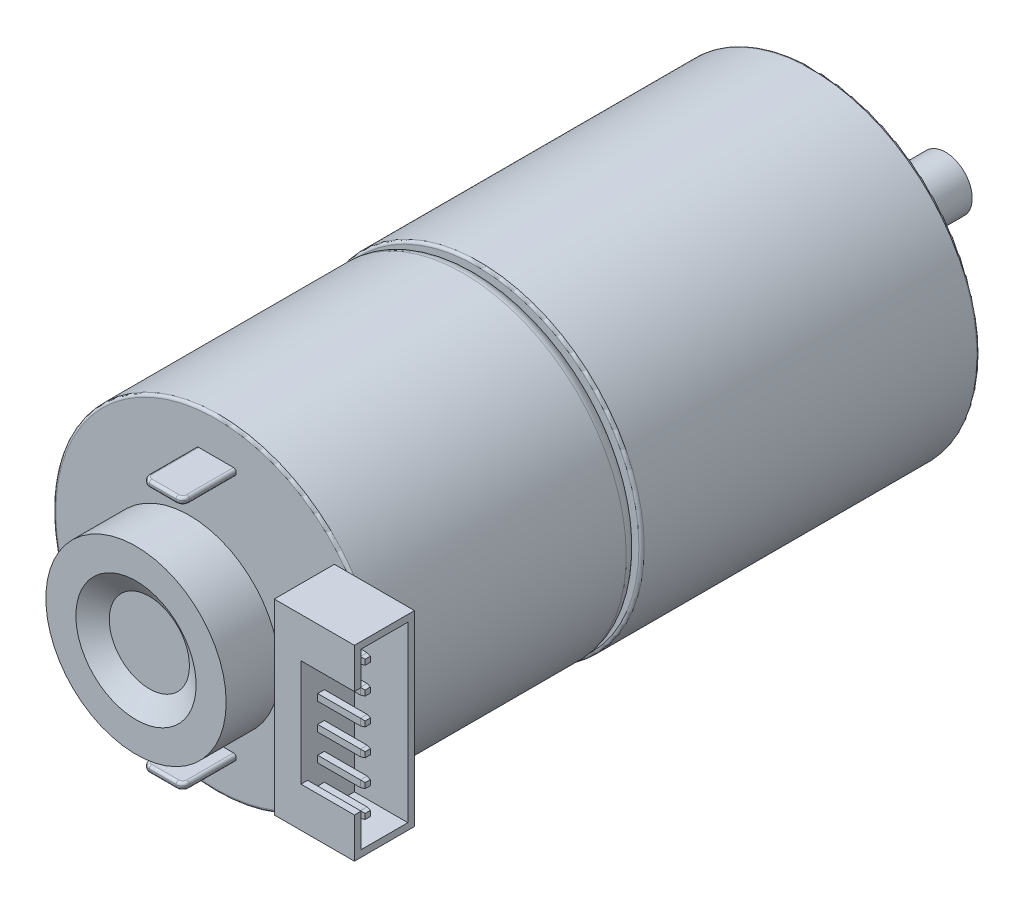
SolidWorks part; units mm, degrees
ref_plane "Front Plane" through (0, 0, 0) normal (0, 0, 1) x (1, 0, 0)
ref_plane "Top Plane" through (0, 0, 0) normal (0, 1, 0) x (1, 0, 0)
ref_plane "Right Plane" through (0, 0, 0) normal (1, 0, 0) x (0, 0, -1)
sketch "Sketch1" plane through (0, 0, 0) normal (0, 0, 1) x (1, 0, 0)
  circle A0 centre (0, 0) radius 12.35
  dimension "D1" = 24.7
extrude "Boss-Extrude1" add sketch "Sketch1" along normal blind 25.3
sketch "Sketch2" plane through (0, 0, 0) normal (1, 0, 0) x (0, 0, -1)
  line L0 (-25.3, 0) -> (-44.8, 0)
  line L1 (-25.3, 12.35) -> (-25.3, -12.35) construction
  line L2 (-44.8, 0) -> (-44.8, 12.2)
  line L3 (-44.8, 12.2) -> (-26.3, 12.2)
  line L4 (-25.3, 11.2) -> (-25.3, 0)
  arc A0 (-26.3, 12.2) -> (-25.3, 11.2) centre (-26.3, 11.2) cw
  point P9 (-25.3, 12.2)
  dimension "D3" = 1
  dimension "D1" = 19.5
  dimension "D2" = 12.2
revolve "Revolve1" add sketch "Sketch2" angle 360 about L0
sketch "Sketch3" plane through (0, 0, 44.8) normal (0, 0, 1) x (1, 0, 0)
  circle A0 centre (0, 0) radius 1
  dimension "D1" = 2
extrude "Boss-Extrude2" add sketch "Sketch3" along normal blind 6
sketch "Sketch4" plane through (0, 0, 44.8) normal (0, 0, 1) x (1, 0, 0)
  line L0 (0, 12.2) -> (0, -12.2) construction
  line L1 (0, 0) -> (-12.2, 0) construction
  line L2 (-1.5, 9) -> (1.5, 9)
  line L3 (-1.5, -9.5) -> (1.5, -9.5)
  line L4 (-1.5, -9.5) -> (-1.5, -9)
  line L5 (-1.5, -9) -> (1.5, -9)
  line L6 (1.5, -9.5) -> (1.5, -9)
  line L7 (-1.5, -9.5) -> (1.5, -9) construction
  line L8 (-1.5, -9) -> (1.5, -9.5) construction
  line L9 (1.5, 9.5) -> (1.5, 9)
  line L10 (-1.5, 9.5) -> (1.5, 9.5)
  line L11 (-1.5, 9.5) -> (-1.5, 9)
  circle A0 centre (0, 0) radius 12.2 construction
  point P8 (0, -9.25)
  dimension "D1" = 0.5
  dimension "D2" = 3
  dimension "D3" = 9
extrude "Boss-Extrude3" add sketch "Sketch4" along normal blind 4
fillet "Fillet2" radius 0.5 4 edges at (-1.5, 9.25, 48.8) (1.5, 9.25, 48.8) (-1.5, -9.25, 48.8) (1.5, -9.25, 48.8)
fillet "Fillet3" radius 0.2 23 edges at (1.5, -9, 46.55) (1.3536, -9, 48.6536) (-1.5, -9, 46.55) (-1.3536, -9, 48.6536) (-1.5, -9.5, 46.55) (-1.3536, -9.5, 48.6536) (1.5, -9.5, 46.55) (1.3536, -9.5, 48.6536) (1.5, 9, 46.55) (-1.5, 9, 46.55) (-1.3536, 9, 48.6536) (0, 9, 48.8) (1.5, 9.5, 46.55) (1.3536, 9.5, 48.6536) (-1.5, 9.5, 46.55) (-1.3536, 9.5, 48.6536) (12.35, 0, 0) (12.35, 0, 25.3) (0, 12.2, 44.8) (0, -9, 48.8) (0, -9.5, 48.8) (1.3536, 9, 48.6536) (0, 9.5, 48.8)
sketch "Sketch5" plane through (0, 0, 0) normal (0, 0, -1) x (-1, 0, 0)
  circle A0 centre (0, 0) radius 3.5
  circle A1 centre (0, 0) radius 12.35 construction
  dimension "D1" = 7
extrude "Boss-Extrude4" add sketch "Sketch5" along normal blind 2.5
fillet "Fillet4" radius 0.2 1 edges at (-3.5, 0, -2.5)
sketch "Sketch6" plane through (0, 0, -2.5) normal (0, 0, -1) x (-1, 0, 0)
  line L0 (1.3229, -1.5) -> (-1.3229, -1.5)
  line L1 (0, -1.5) -> (0, 2) construction
  arc A0 (1.3229, -1.5) -> (-1.3229, -1.5) centre (0, 0) ccw
  dimension "D1" = 4
  dimension "D2" = 3.5
extrude "Boss-Extrude5" add sketch "Sketch6" along normal blind 7.3
sketch "Sketch7" plane through (0, 0, 0) normal (0, 0, -1) x (-1, 0, 0)
  line L0 (0, 8.5) -> (0, -8.5) construction
  circle A0 centre (0, -8.5) radius 1.5
  circle A1 centre (0, 8.5) radius 1.5
  dimension "D1" = 3
  dimension "D2" = 17
hole_wizard "M3 Tapped Hole1" positions "3DSketch1" profile "Sketch8" tap size "M3" standard "ISO"
sketch3d "3DSketch1"
  point P0 (0, -8.5, 0)
  point P3 (0, 8.5, 0)
sketch "Sketch8" plane through (0, -8.5, 0) normal (1, 0, 0) x (0, 1, 0)
  line L0 (0, 0) -> (0, 8.2511)
  line L1 (0, 8.2511) -> (1.25, 7.5)
  line L2 (1.25, 7.5) -> (1.25, 0)
  line L5 (1.25, 0) -> (0, 0)
  line L10 (0, 8.2511) -> (-1.25, 7.5) construction
  line L11 (0, -6.35) -> (0, 107.95) construction
  dimension "Tap Drill Dia." = 2.5
  dimension "Tap Drill Depth" = 7.5
  dimension "Drill Angle" = 118
cosmetic thread "Hole Thread1" parameters "D1"=6, "D2"=3
cosmetic thread "Hole Thread2" parameters "D1"=6, "D2"=3
sketch "Sketch9" plane through (0, 0, 50.8) normal (0, 0, 1) x (1, 0, 0)
  circle A0 centre (0, 0) radius 6.75
  dimension "D1" = 13.5
extrude "Boss-Extrude6" add sketch "Sketch9" against normal blind 4
sketch "Sketch10" plane through (0, 0, 44.8) normal (0, 0, 1) x (1, 0, 0)
  line L0 (8.85, 0) -> (0, 0) construction
  line L1 (8.85, -7) -> (14.85, -7)
  line L2 (8.85, -7) -> (8.85, 7)
  line L3 (8.85, 7) -> (14.85, 7)
  line L4 (14.85, -7) -> (14.85, 7)
  line L5 (12.35, 0) -> (14.85, 0) construction
  circle A0 centre (0, 0) radius 12.35 construction
  dimension "D1" = 14
  dimension "D2" = 6
  dimension "D3" = 2.5
extrude "Boss-Extrude7" add sketch "Sketch10" along normal blind 4.5
sketch "Sketch11" plane through (14.85, 0, 0) normal (1, 0, 0) x (0, 0, -1)
  line L8 (-45.3, -6.5) -> (-45.3, 6.5)
  line L9 (-45.3, 6.5) -> (-48.8, 6.5)
  line L10 (-48.8, 6.5) -> (-48.8, -6.5)
  line L11 (-48.8, -6.5) -> (-45.3, -6.5)
  line L12 (-45.3, -6.5) -> (-45.3, 6.5)
  line L13 (-45.3, 6.5) -> (-48.8, 6.5)
  line L14 (-48.8, 6.5) -> (-48.8, -6.5)
  line L15 (-48.8, -6.5) -> (-45.3, -6.5)
  dimension "D1" = 0.5
extrude "Cut-Extrude1" cut sketch "Sketch11" against normal offset from surface (4 mm away) 2 up to face at (8.85, 0, 47.05)
sketch "Sketch12" plane through (0, 0, 49.3) normal (0, 0, 1) x (1, 0, 0)
  line L0 (14.85, -7) -> (14.85, 7) construction
  line L1 (14.85, -4) -> (10.85, -4)
  line L2 (14.85, -4) -> (14.85, 4)
  line L3 (14.85, 4) -> (10.85, 4)
  line L4 (10.85, -4) -> (10.85, 4)
  line L5 (8.85, 7) -> (8.85, -7) construction
  line L6 (10.85, 0) -> (8.85, 0) construction
  line L7 (8.85, 7) -> (8.85, -7) construction
  dimension "D1" = 8
  dimension "D2" = 2
extrude "Cut-Extrude2" cut sketch "Sketch12" against normal blind 2.5
sketch "Sketch13" plane through (10.85, 0, 0) normal (1, 0, 0) x (0, 0, -1)
  line L0 (-47.8, -6.5) -> (-47.8, 6.5) construction
  line L1 (-48.8, -6.5) -> (-45.3, -6.5) construction
  line L2 (-48.8, 6.5) -> (-45.3, 6.5) construction
  line L3 (-44.8, -7) -> (-44.8, 7) construction
  line L4 (-48.05, -0.75) -> (-48.05, 0.75) construction
  line L5 (-48.05, -5.25) -> (-47.55, -5.25)
  line L6 (-48.05, -5.25) -> (-48.05, -4.75)
  line L7 (-48.05, -4.75) -> (-47.55, -4.75)
  line L8 (-47.55, -5.25) -> (-47.55, -4.75)
  line L9 (-48.05, -5.25) -> (-47.55, -4.75) construction
  line L10 (-48.05, -4.75) -> (-47.55, -5.25) construction
  line L11 (-48.05, -3.25) -> (-47.55, -3.25)
  line L12 (-48.05, -3.25) -> (-48.05, -2.75)
  line L13 (-48.05, -2.75) -> (-47.55, -2.75)
  line L14 (-47.55, -3.25) -> (-47.55, -2.75)
  line L15 (-48.05, -3.25) -> (-47.55, -2.75) construction
  line L16 (-48.05, -2.75) -> (-47.55, -3.25) construction
  line L17 (-48.05, -1.25) -> (-47.55, -1.25)
  line L18 (-48.05, -1.25) -> (-48.05, -0.75)
  line L19 (-48.05, -0.75) -> (-47.55, -0.75)
  line L20 (-47.55, -1.25) -> (-47.55, -0.75)
  line L21 (-48.05, -1.25) -> (-47.55, -0.75) construction
  line L22 (-48.05, -0.75) -> (-47.55, -1.25) construction
  line L23 (-48.05, 0.75) -> (-47.55, 0.75)
  line L24 (-48.05, 0.75) -> (-48.05, 1.25)
  line L25 (-48.05, 1.25) -> (-47.55, 1.25)
  line L26 (-47.55, 0.75) -> (-47.55, 1.25)
  line L27 (-48.05, 0.75) -> (-47.55, 1.25) construction
  line L28 (-48.05, 1.25) -> (-47.55, 0.75) construction
  line L29 (-48.05, 2.75) -> (-47.55, 2.75)
  line L30 (-48.05, 2.75) -> (-48.05, 3.25)
  line L31 (-48.05, 3.25) -> (-47.55, 3.25)
  line L32 (-47.55, 2.75) -> (-47.55, 3.25)
  line L33 (-48.05, 2.75) -> (-47.55, 3.25) construction
  line L34 (-48.05, 3.25) -> (-47.55, 2.75) construction
  line L35 (-48.05, 4.75) -> (-47.55, 4.75)
  line L36 (-48.05, 4.75) -> (-48.05, 5.25)
  line L37 (-48.05, 5.25) -> (-47.55, 5.25)
  line L38 (-47.55, 4.75) -> (-47.55, 5.25)
  line L39 (-48.05, 4.75) -> (-47.55, 5.25) construction
  line L40 (-48.05, 5.25) -> (-47.55, 4.75) construction
  line L41 (-48.05, 0) -> (-49.3, 0) construction
  line L42 (-49.3, 4) -> (-49.3, -4) construction
  point P8 (-47.8, -5)
  point P13 (-47.8, -3)
  point P18 (-47.8, -1)
  point P23 (-47.8, 1)
  point P28 (-47.8, 3)
  point P33 (-47.8, 5)
  dimension "D1" = 3
  dimension "D2" = 2
  dimension "D3" = 2
  dimension "D4" = 2
  dimension "D5" = 2
  dimension "D6" = 2
  dimension "D7" = 0.5
extrude "Boss-Extrude8" add sketch "Sketch13" along normal blind 3.5
chamfer "Chamfer1" distance 0.3 angle 10 24 edges at (14.35, 4.75, 47.8) (14.35, 5, 48.05) (14.35, 5.25, 47.8) (14.35, 5, 47.55) (14.35, 2.75, 47.8) (14.35, 3, 48.05) (14.35, 3.25, 47.8) (14.35, 3, 47.55) (14.35, 0.75, 47.8) (14.35, 1, 48.05) (14.35, 1.25, 47.8) (14.35, 1, 47.55) (14.35, -1.25, 47.8) (14.35, -1, 48.05) (14.35, -0.75, 47.8) (14.35, -1, 47.55) (14.35, -3.25, 47.8) (14.35, -3, 48.05) (14.35, -2.75, 47.8) (14.35, -3, 47.55) (14.35, -4.75, 47.8) (14.35, -5, 48.05) (14.35, -5.25, 47.8) (14.35, -5, 47.55)
sketch "Sketch14" plane through (0, 0, 0) normal (1, 0, 0) x (0, 0, -1)
  line L0 (-50.8, 0) -> (-49.8, 0)
  line L1 (-50.8, 6.75) -> (-50.8, -6.75) construction
  line L2 (-49.8, 0) -> (-49.8, 3)
  line L3 (-49.8, 3) -> (-50.8, 4.5)
  line L4 (-50.8, 4.5) -> (-50.8, 0)
  dimension "D1" = 4.5
  dimension "D2" = 3
  dimension "D3" = 1
revolve "Cut-Revolve1" cut sketch "Sketch14" angle 360 about L0
equation "\"D3@Sketch13\"=\"D2@Sketch13\""
equation "\"D4@Sketch13\"=\"D2@Sketch13\""
equation "\"D5@Sketch13\"=\"D2@Sketch13\""
equation "\"D6@Sketch13\"=\"D2@Sketch13\""
